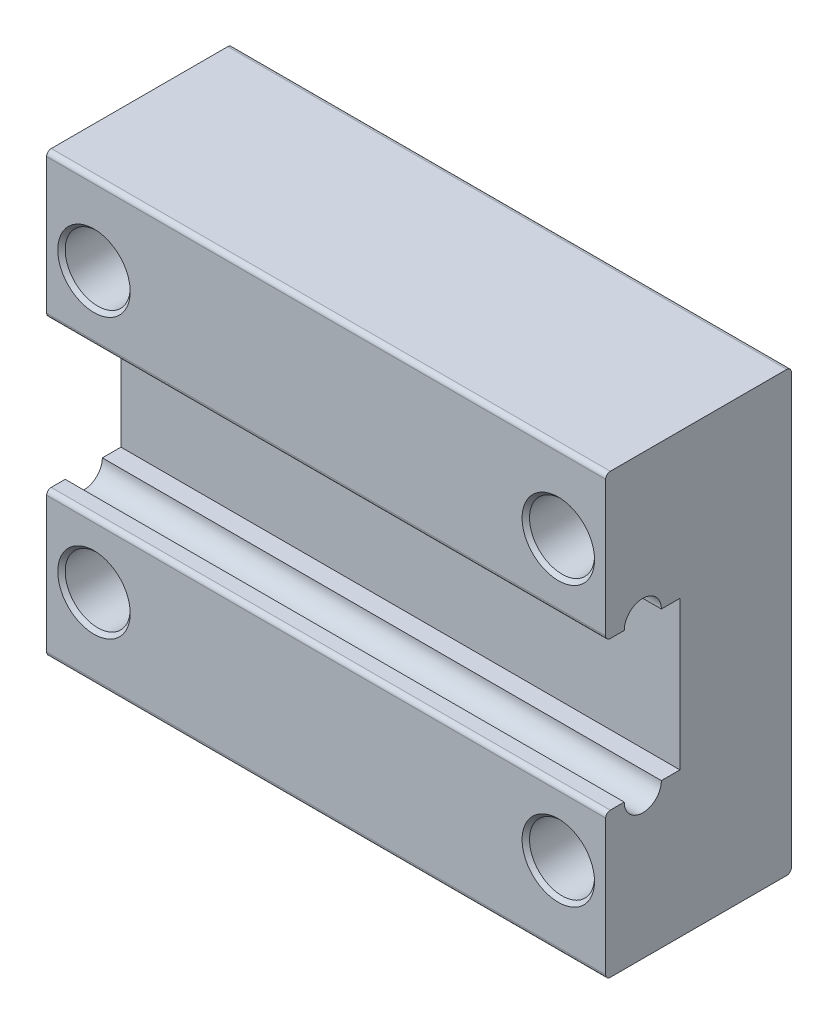
SolidWorks part; units mm, degrees
material "1345 Alloy"
ref_plane "Front Plane" through (0, 0, 0) normal (0, 0, 1) x (1, 0, 0)
ref_plane "Top Plane" through (0, 0, 0) normal (0, 1, 0) x (1, 0, 0)
ref_plane "Right Plane" through (0, 0, 0) normal (1, 0, 0) x (0, 0, -1)
sketch "Sketch1" plane through (0, 0, 0) normal (0, 0, 1) x (1, 0, 0)
  line L0 (0, 0) -> (-50000, 0) construction
  line L1 (22.5, -11.8) -> (-22.5, -11.8)
  line L2 (22.5, -11.8) -> (22.5, 11.8)
  line L3 (22.5, 11.8) -> (-22.5, 11.8)
  line L4 (-22.5, -11.8) -> (-22.5, 11.8)
  line L5 (22.5, -11.8) -> (-22.5, 11.8) construction
  line L6 (22.5, 11.8) -> (-22.5, -11.8) construction
  line L7 (0, 0) -> (0, 50000) construction
  line L9 (-12.5, 7.5) -> (12.5, 7.5) construction
  line L10 (-12.5, 7.5) -> (-12.5, -7.5) construction
  line L11 (-12.5, -7.5) -> (12.5, -7.5) construction
  line L12 (12.5, 7.5) -> (12.5, -7.5) construction
  line L13 (-12.5, 7.5) -> (12.5, -7.5) construction
  line L14 (-12.5, -7.5) -> (12.5, 7.5) construction
  circle A0 centre (-12.5, 7.5) radius 1.75
  circle A1 centre (12.5, 7.5) radius 1.75
  circle A2 centre (12.5, -7.5) radius 1.75
  circle A3 centre (-12.5, -7.5) radius 1.75
  point P0 (0, 0)
  point P10 (0, 0)
  dimension "D5" = 3.5
  dimension "D1" = 45
  dimension "D2" = 23.6
  dimension "D3" = 25
  dimension "D4" = 15
  dimension "D6" = 2
  dimension "D7" = 2
extrude "Boss-Extrude1" add sketch "Sketch1" along normal blind 10
sketch "Sketch2" plane through (22.5, 0, 0) normal (1, 0, 0) x (0, 0, -1)
  line L0 (-10, 0) -> (0, 0) construction
  line L1 (-10, -11.8) -> (-10, 11.8) construction
  line L2 (0, 0) -> (-6, 0) construction
  line L3 (-6, 0) -> (-6, 13) construction
  line L6 (-6, -4) -> (-10, -4)
  line L7 (-6, -4) -> (-6, 4)
  line L8 (-6, 4) -> (-10, 4)
  line L9 (-10, -4) -> (-10, 4)
  line L10 (-6, -4) -> (-10, 4) construction
  line L11 (-6, 4) -> (-10, -4) construction
  circle A0 centre (-8, 4) radius 1
  circle A1 centre (-8, -4) radius 1
  point P9 (-8, 0)
  line M10 (-10, 11.8) -> (-10, -11.8)
  dimension "D2" = 2
  dimension "D1" = 8
  dimension "D3" = 4
extrude "Cut-Extrude1" cut sketch "Sketch2" against normal through all contours L6 A1 L7 L8 A0 M10 | L8 A0
fillet "Fillet1" radius 0.25 16 edges at (-22.5, -11.8, 5) (0, -11.8, 10) (22.5, -11.8, 5) (0, -11.8, 0) (22.5, 11.8, 5) (0, 11.8, 10) (-22.5, 11.8, 5) (0, 11.8, 0) (22.5, 0, 0) (-22.5, 0, 0) (-22.5, 7.9, 10) (-22.5, -7.9, 10) (22.5, -7.9, 10) (22.5, 7.9, 10) (0, 4, 10) (0, -4, 10)
chamfer "Chamfer1" distance 0.2 angle 45 8 edges at (14.25, -7.5, 0) (14.25, -7.5, 10) (-10.75, -7.5, 0) (-10.75, -7.5, 10) (14.25, 7.5, 0) (14.25, 7.5, 10) (-10.75, 7.5, 0) (-10.75, 7.5, 10)
sketch "Sketch3" plane through (0, 0, 0) normal (0, 0, -1) x (-1, 0, 0)
  line L2 (-15.05, 17.4912) -> (-26.0551, 17.4912)
  line L3 (-15.05, 17.4912) -> (-15.05, -15.0256)
  line L4 (-15.05, -15.0256) -> (-26.0551, -15.0256)
  line L5 (-26.0551, 17.4912) -> (-26.0551, -15.0256)
  line L6 (25.05, 17.4912) -> (15.05, 17.4912)
  line L7 (25.05, 17.4912) -> (25.05, -18.6261)
  line L8 (25.05, -18.6261) -> (15.05, -18.6261)
  line L9 (15.05, 17.4912) -> (15.05, -18.6261)
  dimension "D1" = 15.05
  dimension "D2" = 15.05
  dimension "D3" = 10
extrude "Cut-Extrude2" cut sketch "Sketch3" against normal blind 10
